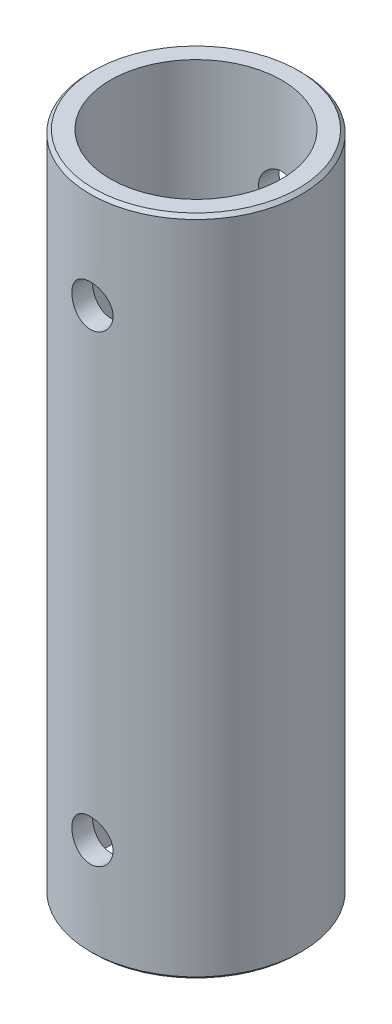
SolidWorks part; units mm, degrees
ref_plane "Front Plane" through (0, 0, 0) normal (0, 0, 1) x (1, 0, 0)
ref_plane "Top Plane" through (0, 0, 0) normal (0, 1, 0) x (1, 0, 0)
ref_plane "Right Plane" through (0, 0, 0) normal (1, 0, 0) x (0, 0, -1)
sketch "Sketch1" plane through (0, 0, 0) normal (0, 1, 0) x (1, 0, 0)
  circle A0 centre (0, 0) radius 7.94
  circle A1 centre (0, 0) radius 6.44
  dimension "D1" = 15.88
  dimension "D2" = 1.5
extrude "Boss-Extrude1" add sketch "Sketch1" along normal blind 49.82
chamfer "Chamfer1" distance 0.25 angle 45 2 edges at (0, 0, 7.94) (0, 49.82, 7.94)
sketch "Sketch2" plane through (0, 0, -5.85) normal (0, 0, -1) x (-1, 0, 0)
  circle A0 centre (0.0002, 7.5) radius 1.55 construction
  circle A1 centre (0.0002, 7.5) radius 1.55
  spline S0 degree 3 poles (1.5502, 42.32) (1.5502, 45.42) (-1.5498, 45.42) (-1.5498, 42.32) (-1.5498, 39.22) (1.5502, 39.22) (1.5502, 42.32) (1.5502, 45.42) (-1.5498, 45.42) knots -0.5 0 0 0 0.5 0.5 0.5 1 1 1 1.5 1.5 1.5 weights 1 0.333333 0.333333 1 0.333333 0.333333 1 0.333333 0.333333 only from (1.5502, 42.32) to (1.5502, 42.32) construction
  spline S1 degree 3 poles (1.5502, 42.32) (1.5502, 45.42) (-1.5498, 45.42) (-1.5498, 42.32) (-1.5498, 39.22) (1.5502, 39.22) (1.5502, 42.32) (1.5502, 45.42) (-1.5498, 45.42) knots -0.5 0 0 0 0.5 0.5 0.5 1 1 1 1.5 1.5 1.5 weights 1 0.333333 0.333333 1 0.333333 0.333333 1 0.333333 0.333333 only from (1.5502, 42.32) to (1.5502, 42.32)
extrude "Cut-Extrude1" cut sketch "Sketch2" against normal through all both and the other way through all
